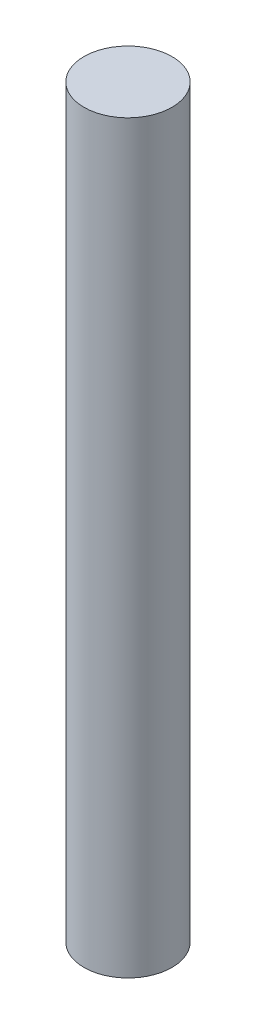
SolidWorks part; units mm, degrees
ref_plane "Front Plane" through (0, 0, 0) normal (0, 0, 1) x (1, 0, 0)
ref_plane "Top Plane" through (0, 0, 0) normal (0, 1, 0) x (1, 0, 0)
ref_plane "Right Plane" through (0, 0, 0) normal (1, 0, 0) x (0, 0, -1)
sketch "Sketch1" plane through (0, 0, 0) normal (0, 1, 0) x (1, 0, 0)
  circle A0 centre (0, 0) radius 0.75
  dimension "D1" = 1.5
extrude "Boss-Extrude1" add sketch "Sketch1" along normal blind 12.7
